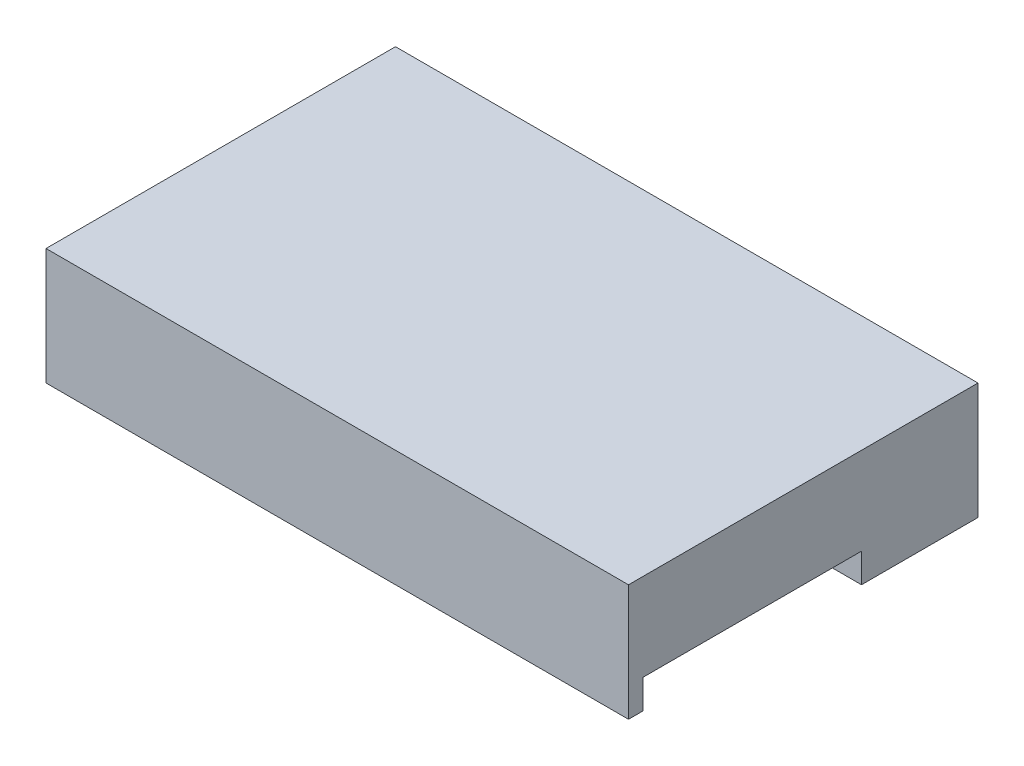
SolidWorks part; units mm, degrees
ref_plane "Front Plane" through (0, 0, 0) normal (0, 0, 1) x (1, 0, 0)
ref_plane "Top Plane" through (0, 0, 0) normal (0, 1, 0) x (1, 0, 0)
ref_plane "Right Plane" through (0, 0, 0) normal (1, 0, 0) x (0, 0, -1)
sketch "Sketch2" plane through (0, 0, 0) normal (0, 1, 0) x (1, 0, 0)
  line L1 (-10, -6) -> (10, -6)
  line L2 (-10, -6) -> (-10, 6)
  line L3 (-10, 6) -> (10, 6)
  line L4 (10, -6) -> (10, 6)
  line L5 (-10, -6) -> (10, 6) construction
  line L6 (-10, 6) -> (10, -6) construction
  point P0 (0, 0)
  dimension "D1" = 12
  dimension "D2" = 20
extrude "Boss-Extrude1" add sketch "Sketch2" along normal blind 4
sketch "Sketch3" plane through (0, 0, 0) normal (0, -1, 0) x (1, 0, 0)
  line L0 (10, 6) -> (10, -6) construction
  line L1 (-10, 6) -> (10, 6)
  line L2 (-10, 6) -> (-10, -2)
  line L3 (-10, -2) -> (10, -2)
  line L4 (10, 6) -> (10, -2)
  dimension "D1" = 8
extrude "Cut-Extrude1" cut sketch "Sketch3" against normal blind 1
sketch "Sketch4" plane through (0, 1, 0) normal (0, -1, 0) x (1, 0, 0)
  line L0 (10, -2) -> (10, 6) construction
  line L1 (-10, 6) -> (10, 6)
  line L2 (-10, 6) -> (-10, 5.5)
  line L3 (-10, 5.5) -> (10, 5.5)
  line L4 (10, 6) -> (10, 5.5)
  dimension "D1" = 0.5
extrude "Boss-Extrude2" add sketch "Sketch4" along normal blind 1
